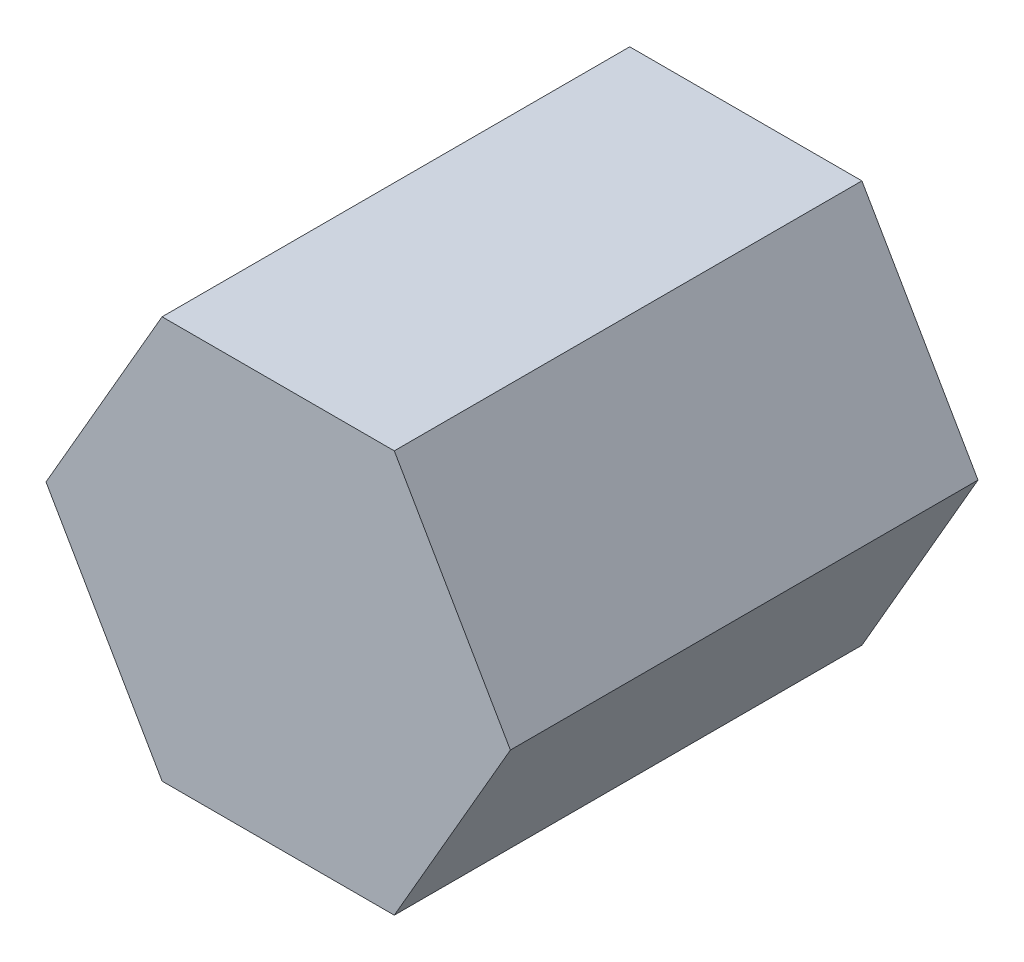
SolidWorks part; units mm, degrees
ref_plane "Front Plane" through (0, 0, 0) normal (0, 0, 1) x (1, 0, 0)
ref_plane "Top Plane" through (0, 0, 0) normal (0, 1, 0) x (1, 0, 0)
ref_plane "Right Plane" through (0, 0, 0) normal (1, 0, 0) x (0, 0, -1)
sketch "Sketch1" plane through (0, 0, 0) normal (0, 0, 1) x (1, 0, 0)
  line L0 (-0.4435, -0.309) -> (5.8623, -0.309)
  line L1 (5.8623, -0.309) -> (9.0152, -5.77)
  line L2 (9.0152, -5.77) -> (5.8623, -11.231)
  line L3 (5.8623, -11.231) -> (-0.4435, -11.231)
  line L4 (-0.4435, -11.231) -> (-3.5964, -5.77)
  line L5 (-3.5964, -5.77) -> (-0.4435, -0.309)
  dimension "D1" = 120
  dimension "D2" = 120
  dimension "D3" = 120
  dimension "D4" = 120
  dimension "D5" = 10.922
extrude "Boss-Extrude1" add sketch "Sketch1" along normal blind 12.7
